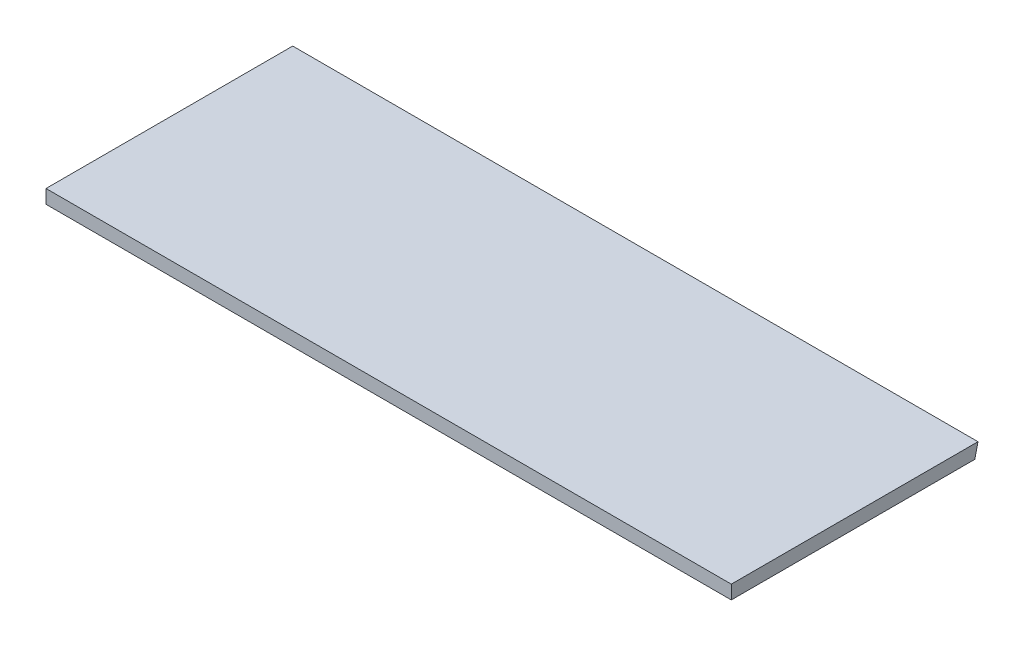
SolidWorks part; units mm, degrees
ref_plane "Ön Düzlem" through (0, 0, 0) normal (0, 0, 1) x (1, 0, 0)
ref_plane "Üst Düzlem" through (0, 0, 0) normal (0, 1, 0) x (1, 0, 0)
ref_plane "Sağ Düzlem" through (0, 0, 0) normal (1, 0, 0) x (0, 0, -1)
sketch "Sketch2" plane through (0, 0, 0) normal (0, 1, 0) x (1, 0, 0)
  line L1 (-250, -90) -> (250, -90)
  line L2 (-250, -90) -> (-250, 90)
  line L3 (-250, 90) -> (250, 90)
  line L4 (250, -90) -> (250, 90)
  line L5 (-250, -90) -> (250, 90) construction
  line L6 (-250, 90) -> (250, -90) construction
  point P0 (0, 0)
  dimension "D1" = 500
  dimension "D2" = 180
extrude "Boss-Extrude1" add sketch "Sketch2" along normal blind 10
sketch "Sketch4" plane through (250, 0, 0) normal (1, 0, 0) x (0, 0, -1)
  line L0 (90, 10) -> (87.6913, 0)
  line L2 (-90, 0) -> (90, 0) construction
  line L3 (90, 10) -> (90, 0)
  line L7 (87.6913, 0) -> (90, 0)
  dimension "D1" = 13
extrude "Cut-Extrude4" cut sketch "Sketch4" against normal through all
